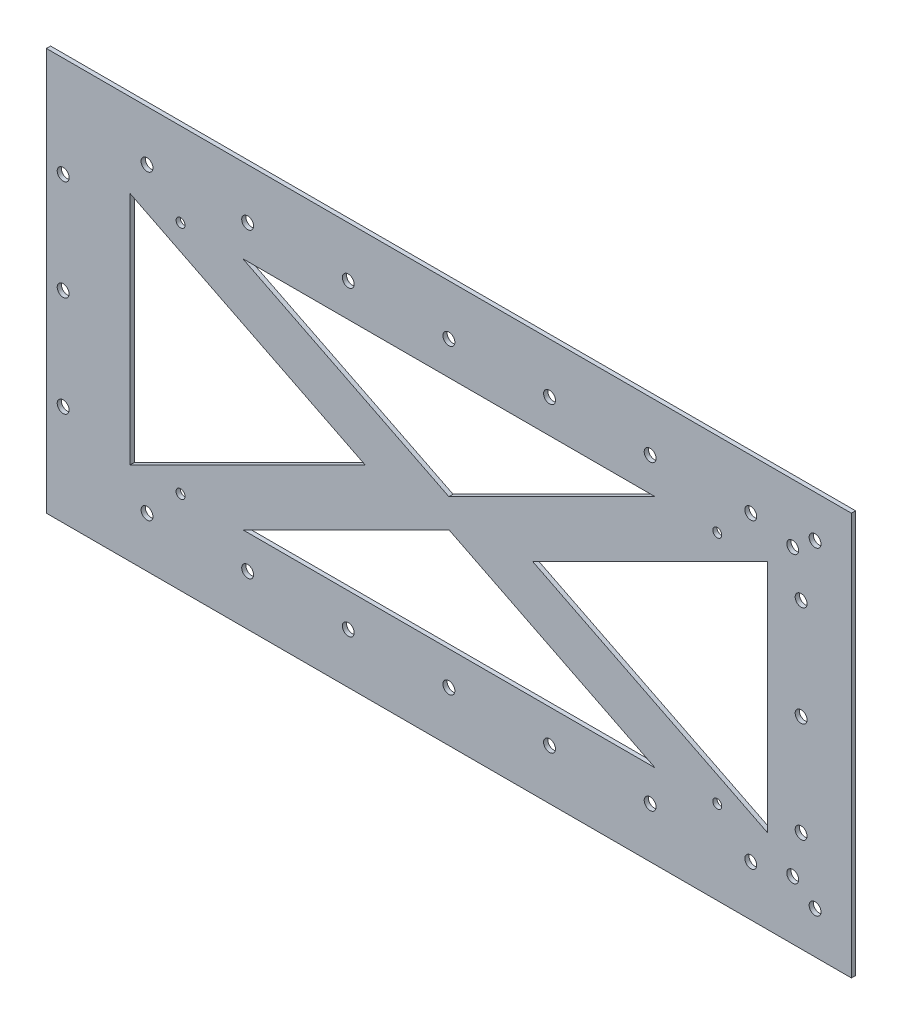
SolidWorks part; units mm, degrees
ref_plane "Front Plane" through (0, 0, 0) normal (0, 0, 1) x (1, 0, 0)
ref_plane "Top Plane" through (0, 0, 0) normal (0, 1, 0) x (1, 0, 0)
ref_plane "Right Plane" through (0, 0, 0) normal (1, 0, 0) x (0, 0, -1)
sketch "Sketch1" plane through (0, 0, 0) normal (0, 0, 1) x (1, 0, 0)
  line L0 (-120.65, 44.45) -> (-120.65, -44.45)
  line L1 (-152.4, -76.2) -> (152.4, -76.2)
  line L2 (-152.4, -76.2) -> (-152.4, 76.2)
  line L3 (-152.4, 76.2) -> (152.4, 76.2)
  line L4 (152.4, -76.2) -> (152.4, 76.2)
  line L5 (-152.4, -76.2) -> (152.4, 76.2) construction
  line L6 (-152.4, 76.2) -> (152.4, -76.2) construction
  line L7 (-120.65, -44.45) -> (-31.75, 0)
  line L8 (-31.75, 0) -> (-120.65, 44.45)
  line L9 (-78.0529, 44.45) -> (78.0529, 44.45)
  line L10 (78.0529, 44.45) -> (0, 5.4235)
  line L11 (0, 5.4235) -> (-78.0529, 44.45)
  line L12 (0, -5.4235) -> (-78.0529, -44.45)
  line L13 (-78.0529, -44.45) -> (78.0529, -44.45)
  line L14 (78.0529, -44.45) -> (0, -5.4235)
  line L15 (31.75, 0) -> (120.65, 44.45)
  line L16 (120.65, 44.45) -> (120.65, -44.45)
  line L17 (120.65, -44.45) -> (31.75, 0)
  point P0 (0, 0)
  dimension "D1" = 304.8
  dimension "D2" = 152.4
  dimension "D3" = 31.75
  dimension "D4" = 31.75
  dimension "D5" = 31.75
  dimension "D6" = 31.75
  dimension "D7" = 19.05
  dimension "D8" = 19.05
extrude "Boss-Extrude1" add sketch "Sketch1" along normal mid plane 1.5875
sketch "Sketch2" plane through (0, 0, 0.7937) normal (0, 0, 1) x (1, 0, 0)
  line L0 (133.355, 38.1) -> (133.355, 0) construction
  line L1 (133.355, 0) -> (133.355, -38.1) construction
  line L2 (152.4, -76.2) -> (152.4, 76.2) construction
  line L3 (-152.4, -76.2) -> (152.4, -76.2) construction
  line L4 (152.4, 76.2) -> (-152.4, 76.2) construction
  line L5 (0, 0) -> (133.355, 0) construction
  circle A0 centre (133.355, 38.1) radius 2.25
  circle A1 centre (133.355, 0) radius 2.25
  circle A2 centre (133.355, -38.1) radius 2.25
  circle A3 centre (114.3, 57.15) radius 2.25
  circle A4 centre (114.3, -57.15) radius 2.25
  circle A5 centre (76.2, -57.15) radius 2.25
  circle A6 centre (76.2, 57.15) radius 2.25
  circle A7 centre (38.1, -57.15) radius 2.25
  circle A8 centre (38.1, 57.15) radius 2.25
  circle A9 centre (0, -57.15) radius 2.25
  circle A10 centre (0, 57.15) radius 2.25
  circle A11 centre (-38.1, -57.15) radius 2.25
  circle A12 centre (-38.1, 57.15) radius 2.25
  circle A13 centre (-76.2, -57.15) radius 2.25
  circle A14 centre (-76.2, 57.15) radius 2.25
  circle A15 centre (-114.3, -57.15) radius 2.25
  circle A16 centre (-114.3, 57.15) radius 2.25
  circle A17 centre (130.175, 53.975) radius 2.25
  circle A18 centre (138.6417, 60.325) radius 2.25
  circle A19 centre (130.175, -53.975) radius 2.25
  circle A20 centre (138.6417, -60.325) radius 2.25
  point P46 (133.355, 0)
  dimension "D1" = 4.5
  dimension "D4" = 38.1
  dimension "D9" = 13.7583
  dimension "D2" = 38.1
  dimension "D3" = 19.045
  dimension "D5" = 19.05
  dimension "D6" = 19.05
  dimension "D8" = 38.1
  dimension "D10" = 15.875
  dimension "D11" = 6.35
  dimension "D12" = 8.4667
  dimension "D7" = 7
extrude "Cut-Extrude1" cut sketch "Sketch2" against normal through all
sketch "Sketch3" plane through (0, 0, 0.7937) normal (0, 0, 1) x (1, 0, 0)
  line L0 (-152.4, 76.2) -> (-152.4, -76.2) construction
  line L1 (-146.05, 38.1) -> (-146.05, 0) construction
  line L2 (-146.05, 0) -> (-146.05, -38.1) construction
  circle A0 centre (-146.05, 38.1) radius 2.25
  circle A1 centre (-146.05, -38.1) radius 2.25
  circle A2 centre (-146.05, 0) radius 2.25
  dimension "D1" = 4.5
  dimension "D2" = 6.35
  dimension "D3" = 38.1
extrude "Cut-Extrude2" cut sketch "Sketch3" against normal through all
sketch "Sketch4" plane through (0, 0, 0.7937) normal (0, 0, 1) x (1, 0, 0)
  line L1 (-101.6, -44.45) -> (101.6, -44.45) construction
  line L2 (-101.6, -44.45) -> (-101.6, 44.45) construction
  line L3 (-101.6, 44.45) -> (101.6, 44.45) construction
  line L4 (101.6, -44.45) -> (101.6, 44.45) construction
  line L5 (-101.6, -44.45) -> (101.6, 44.45) construction
  line L6 (-101.6, 44.45) -> (101.6, -44.45) construction
  circle A0 centre (-101.6, -44.45) radius 1.7
  circle A1 centre (101.6, -44.45) radius 1.7
  circle A2 centre (101.6, 44.45) radius 1.7
  circle A3 centre (-101.6, 44.45) radius 1.7
  point P0 (0, 0)
  dimension "D1" = 3.4
  dimension "D2" = 203.2
  dimension "D3" = 88.9
extrude "Cut-Extrude3" cut sketch "Sketch4" against normal through all
